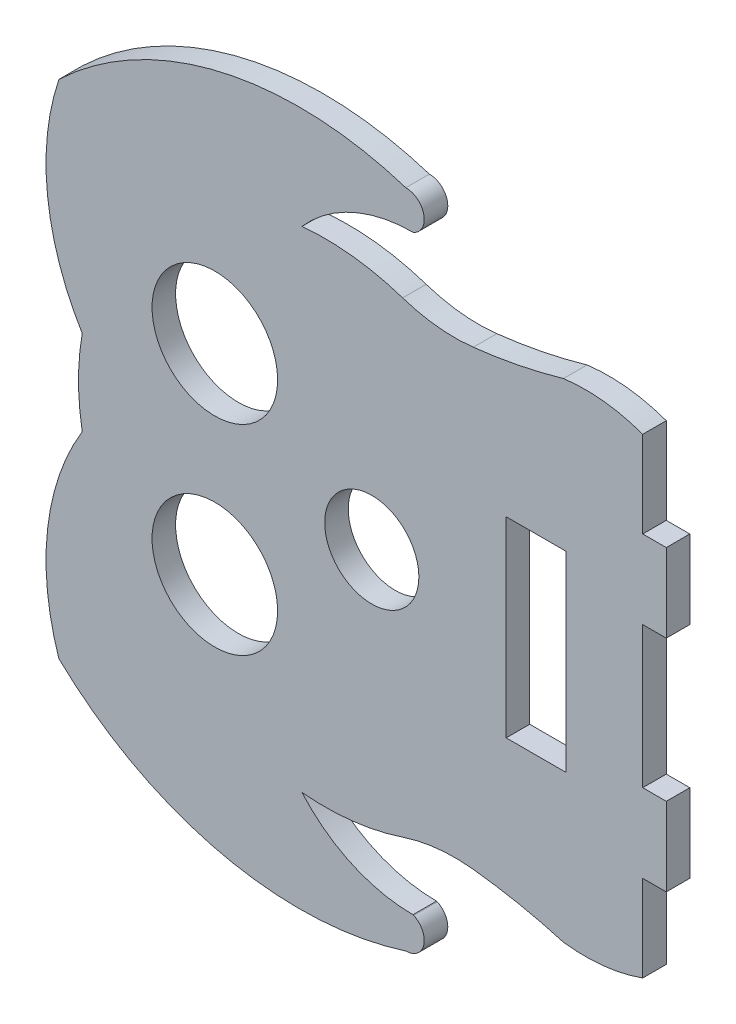
SolidWorks part; units mm, degrees
ref_plane "Front Plane" through (0, 0, 0) normal (0, 0, 1) x (1, 0, 0)
ref_plane "Top Plane" through (0, 0, 0) normal (0, 1, 0) x (1, 0, 0)
ref_plane "Right Plane" through (0, 0, 0) normal (1, 0, 0) x (0, 0, -1)
sketch "Sketch2" plane through (0, 0, 0) normal (0, 0, 1) x (1, 0, 0)
  line L0 (81.0321, 50.1813) -> (81.0321, 60.1813)
  line L1 (81.0321, 60.1813) -> (78.0321, 60.1813)
  line L2 (78.0321, 60.1813) -> (78.0321, 71.1813)
  line L15 (78.0321, 11.1813) -> (78.0321, 22.1813)
  line L16 (78.0321, 22.1813) -> (81.0321, 22.1813)
  line L17 (81.0321, 22.1813) -> (81.0321, 32.1813)
  line L18 (81.0321, 32.1813) -> (78.0321, 32.1813)
  line L19 (78.0321, 32.1813) -> (78.0321, 50.1813)
  line L20 (78.0321, 50.1813) -> (81.0321, 50.1813)
  line L49 (78.0321, 41.1813) -> (23.507, 41.1813) construction
  line L50 (60.632, 41.1813) -> (68.232, 41.1813) construction
  line L51 (68.232, 53.3813) -> (60.632, 53.3813)
  line L52 (68.232, 53.3813) -> (68.232, 28.9813)
  line L53 (68.232, 28.9813) -> (60.632, 28.9813)
  line L54 (60.632, 53.3813) -> (60.632, 28.9813)
  circle A0 centre (23.507, 53.9313) radius 8
  circle A1 centre (43.507, 41.1813) radius 6
  circle A2 centre (23.507, 28.4313) radius 8
  arc A12 (47.4371, 70.9365) -> (34.6136, 72.416) centre (37.507, 41.1813) ccw
  arc A13 (6.6103, 46.6008) -> (3.6415, 73.1505) centre (33.7401, 63.0753) cw
  arc A14 (3.6415, 73.1505) -> (47.8479, 83.2972) centre (34.2837, 41.0216) cw
  arc A15 (47.8479, 83.2972) -> (48.857, 78.8669) centre (47.8663, 80.9713) cw
  arc A16 (48.857, 78.8669) -> (48.7553, 78.8353) centre (56.7811, 53.1787) ccw
  arc A17 (48.7553, 78.8353) -> (34.6136, 72.416) centre (48.758, 60.0425) ccw
  arc A18 (56.4384, 69.9888) -> (67.9362, 72.2842) centre (48.6767, 138.8111) ccw
  arc A19 (67.9362, 72.2842) -> (78.0321, 71.1813) centre (70.7118, 50.9322) cw
  arc A20 (6.6103, 35.7618) -> (3.6415, 9.2121) centre (33.7401, 19.2873) ccw
  arc A21 (3.6415, 9.2121) -> (47.8479, -0.9345) centre (34.2837, 41.341) ccw
  arc A22 (47.8479, -0.9345) -> (48.857, 3.4957) centre (47.8663, 1.3913) ccw
  arc A23 (48.857, 3.4957) -> (48.7553, 3.5274) centre (56.7811, 29.1839) cw
  arc A24 (48.7553, 3.5274) -> (34.6136, 9.9466) centre (48.758, 22.3201) cw
  arc A25 (67.9362, 10.0784) -> (78.0321, 11.1813) centre (70.7118, 31.4304) ccw
  arc A26 (56.4384, 12.3738) -> (67.9362, 10.0784) centre (48.6767, -56.4485) cw
  arc A27 (56.4384, 69.9888) -> (47.4371, 70.9365) centre (54.085, 90.8565) cw
  arc A28 (56.4384, 12.3738) -> (47.4371, 11.4261) centre (54.085, -8.4939) ccw
  arc A29 (6.6103, 46.6008) -> (6.6103, 35.7618) centre (37.507, 41.1813) ccw
  arc A30 (34.6136, 9.9466) -> (47.4371, 11.4261) centre (37.507, 41.1813) ccw
  point P89 (50.8177, 69.5856)
  point P92 (50.8177, 12.777)
  dimension "D2" = 21
  dimension "D3" = 21
  dimension "D4" = 12.75
  dimension "D5" = 12.75
  dimension "D8" = 17.125
  dimension "D1" = 11
  dimension "D6" = 24.4
  dimension "D7" = 7.6
extrude "Boss-Extrude1" add sketch "Sketch2" along normal blind 3
